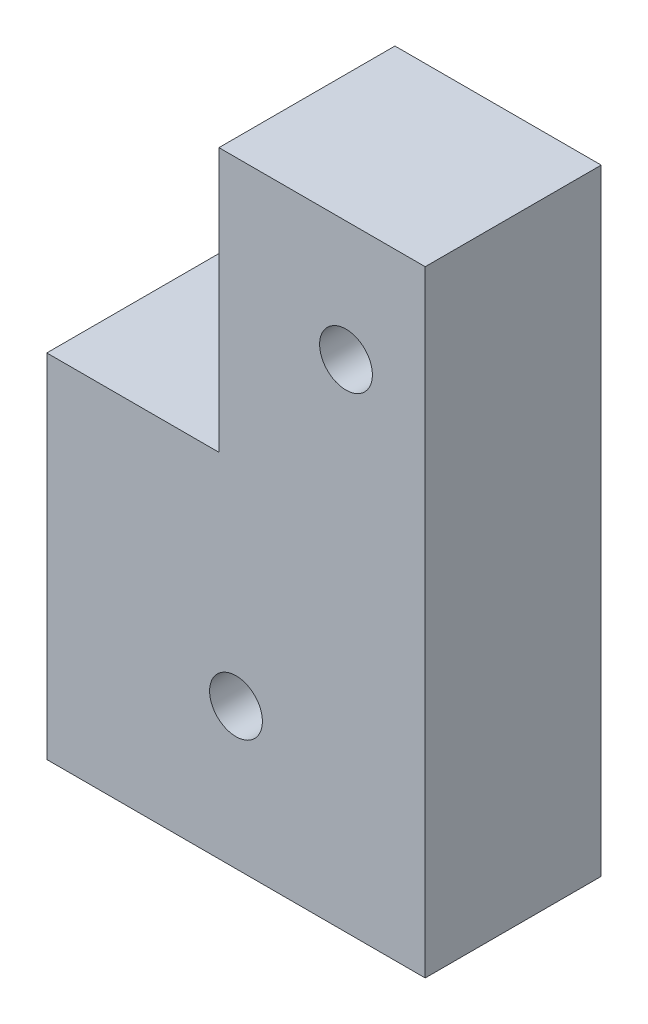
SolidWorks part; units mm, degrees
ref_plane "前视基准面" through (0, 0, 0) normal (0, 0, 1) x (1, 0, 0)
ref_plane "上视基准面" through (0, 0, 0) normal (0, 1, 0) x (1, 0, 0)
ref_plane "右视基准面" through (0, 0, 0) normal (1, 0, 0) x (0, 0, -1)
sketch "草图1" plane through (0, 0, 0) normal (0, 0, 1) x (1, 0, 0)
  line L0 (7.8504, 8.6035) -> (16.235, 8.6035)
  line L1 (16.235, 16.6287) -> (16.235, 8.6035)
  line L3 (26.9542, 20.7752) -> (26.9542, -17.4039)
  line L20 (16.235, 20.7752) -> (16.235, 16.6287)
  line L21 (7.8504, 8.6035) -> (5.4542, 8.6035)
  line L22 (5.4542, 8.6035) -> (5.4542, -17.4039)
  line L23 (5.4542, -17.4039) -> (26.9542, -17.4039)
  line L29 (26.9542, 20.7752) -> (16.235, 20.7752)
  dimension "D1" = 21.5
extrude "凸台-拉伸1" add sketch "草图1" along normal blind 10
sketch "草图2" plane through (0, 8.6035, 0) normal (0, 1, 0) x (1, 0, 0)
  line L4 (16.235, 0) -> (5.4542, 0)
  line L5 (5.4542, 0) -> (5.4542, -10)
  line L6 (5.4542, -10) -> (16.235, -10)
  line L7 (16.235, -10) -> (16.235, 0)
  line L8 (16.235, 0) -> (5.4542, 0)
  line L9 (5.4542, 0) -> (5.4542, -10)
  line L10 (5.4542, -10) -> (16.235, -10)
  line L11 (16.235, -10) -> (16.235, 0)
  dimension "D1" = 0
extrude "切除-拉伸1" cut sketch "草图2" against normal blind 6
sketch "草图3" plane through (16.235, 0, 0) normal (-1, 0, 0) x (0, 0, 1)
  line L4 (0, 20.7752) -> (0, 2.6035)
  line L5 (0, 2.6035) -> (10, 2.6035)
  line L6 (10, 2.6035) -> (10, 20.7752)
  line L7 (10, 20.7752) -> (0, 20.7752)
  line L8 (0, 20.7752) -> (0, 2.6035)
  line L9 (0, 2.6035) -> (10, 2.6035)
  line L10 (10, 2.6035) -> (10, 20.7752)
  line L11 (10, 20.7752) -> (0, 20.7752)
  dimension "D1" = 0
extrude "凸台-拉伸2" add sketch "草图3" along normal blind 1
sketch "草图4" plane through (0, 0, 10) normal (0, 0, 1) x (1, 0, 0)
  line L0 (26.9542, -17.4039) -> (26.9542, 20.7752) construction
  circle A0 centre (16.2042, -9.4039) radius 1.5
  circle A1 centre (22.4542, 10.7752) radius 1.5
  point P0 (0, 0)
  dimension "D3" = 3
  dimension "D4" = 3
  dimension "D1" = 4.5
extrude "切除-拉伸2" cut sketch "草图4" against normal through all
sketch "草图5" plane through (0, 20.7752, 0) normal (0, 1, 0) x (1, 0, 0)
  line L4 (26.9542, 0) -> (15.235, 0)
  line L5 (15.235, 0) -> (15.235, -10)
  line L6 (15.235, -10) -> (26.9542, -10)
  line L7 (26.9542, -10) -> (26.9542, 0)
  line L8 (26.9542, 0) -> (15.235, 0)
  line L9 (15.235, 0) -> (15.235, -10)
  line L10 (15.235, -10) -> (26.9542, -10)
  line L11 (26.9542, -10) -> (26.9542, 0)
  dimension "D1" = 0
extrude "切除-拉伸3" cut sketch "草图5" against normal blind 3.18
